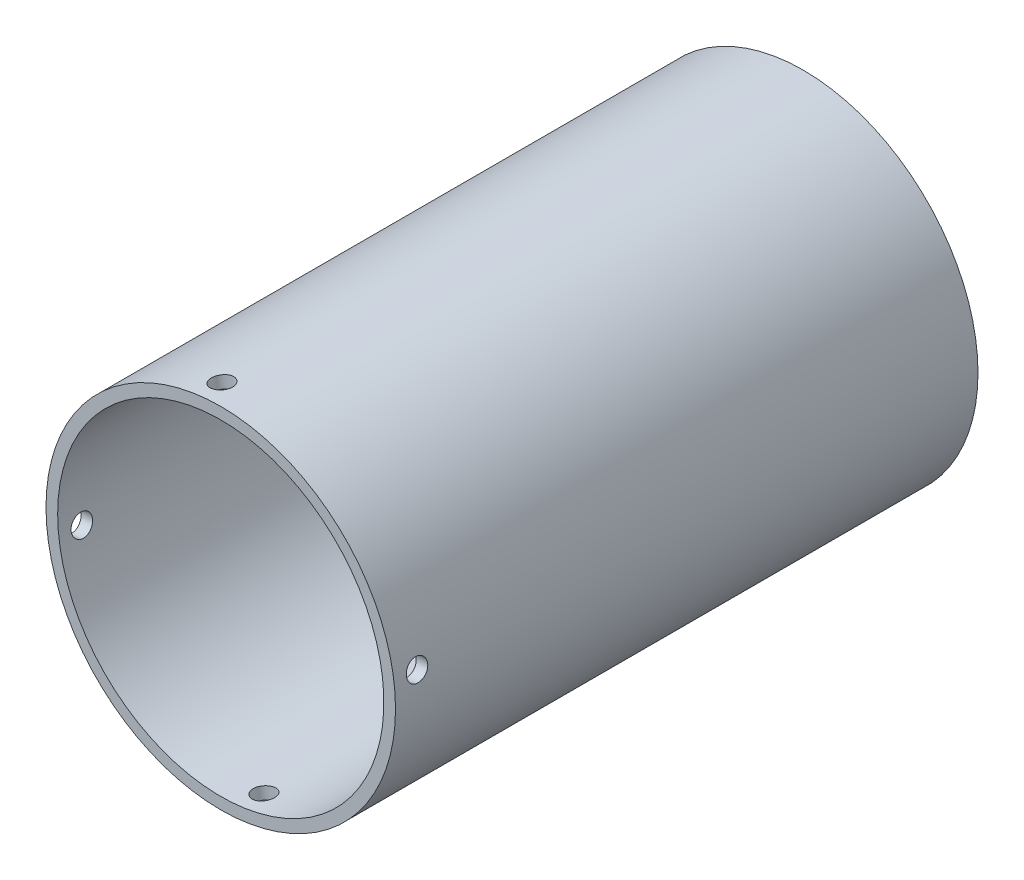
SolidWorks part; units mm, degrees
ref_plane "Plan de face" through (0, 0, 0) normal (0, 0, 1) x (1, 0, 0)
ref_plane "Plan de dessus" through (0, 0, 0) normal (0, 1, 0) x (1, 0, 0)
ref_plane "Plan de droite" through (0, 0, 0) normal (1, 0, 0) x (0, 0, -1)
sketch "Esquisse1" plane through (0, 0, 0) normal (0, 0, 1) x (1, 0, 0)
  circle A0 centre (0, 0) radius 45
  dimension "D1" = 90
extrude "Boss.-Extru.1" add sketch "Esquisse1" along normal blind 150
sketch "Esquisse2" plane through (0, 0, 0) normal (0, 0, -1) x (-1, 0, 0)
  circle A0 centre (0, 0) radius 42
  dimension "D1" = 84
extrude "Enlèv. mat.-Extru.1" cut sketch "Esquisse2" against normal blind 150
sketch "Esquisse3" plane through (0, 0, 0) normal (0, 0, -1) x (-1, 0, 0)
  line L0 (0, 0) -> (59.2001, 0) construction
hole_wizard "Dégagement M51" positions "Esquisse3D1" profile "Esquisse4" hole size "M5" standard "ISO" end condition through all
sketch3d "Esquisse3D1"
  line L0 (-44.649, -5.6094, 144.1078) -> (-44.649, -5.6094, 268.2803) construction
  line L2 (0, 0, 0) -> (-59.2001, 0, 0) construction
  point P0 (-44.649, -5.6094, 144.1078)
  point P9 (-29.6, 0, 0)
  dimension "D1" = 145
sketch "Esquisse4" plane through (-44.649, -5.6094, 144.1078) normal (0, 0, 1) x (0.1247, -0.9922, 0)
  line L0 (0, 0) -> (0, 95.2585)
  line L1 (0, 95.2585) -> (2.75, 95.2585)
  line L2 (2.75, 95.2585) -> (2.75, 0)
  line L5 (2.75, 0) -> (0, 0)
  line L11 (0, -6.35) -> (0, 107.95) construction
  dimension "Diamètre du perçage jusqu'au prochain" = 5.5
  dimension "Profondeur du perçage jusqu'au prochain" = 95.2585
pattern_circular "Répétition circulaire1" count 2 over 90 about axis through (0, 0, 0) along (0, 0, 1) of "Dégagement M51"
